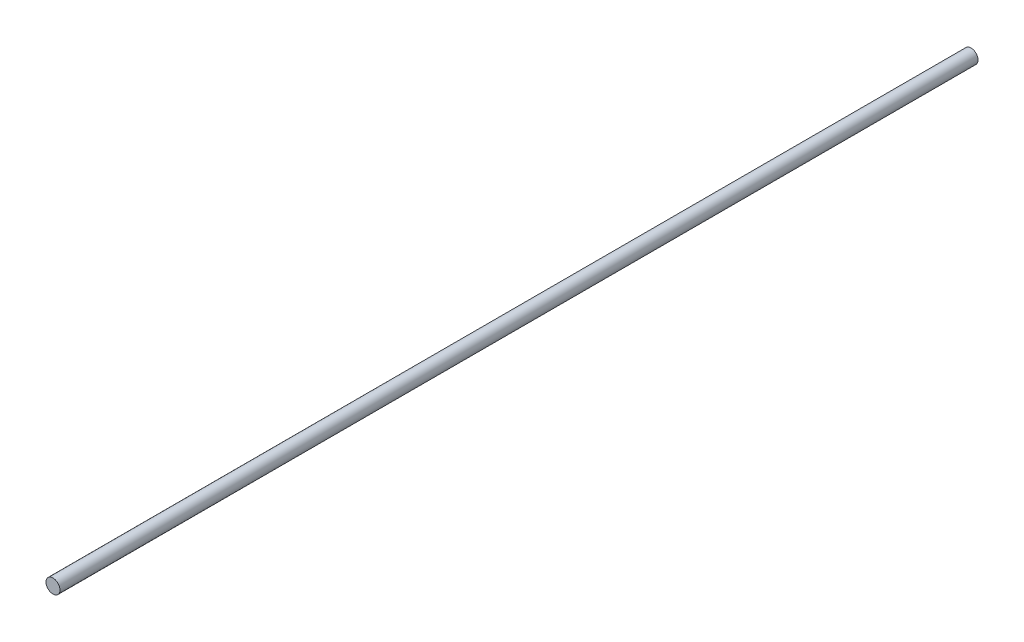
SolidWorks part; units mm, degrees
ref_plane "Front Plane" through (0, 0, 0) normal (0, 0, 1) x (1, 0, 0)
ref_plane "Top Plane" through (0, 0, 0) normal (0, 1, 0) x (1, 0, 0)
ref_plane "Right Plane" through (0, 0, 0) normal (1, 0, 0) x (0, 0, -1)
sketch "Sketch1" plane through (0, 0, 0) normal (0, 0, 1) x (1, 0, 0)
  circle A0 centre (0, 0) radius 4.826
  dimension "D1" = 9.652
extrude "Boss-Extrude1" add sketch "Sketch1" along normal blind 635
